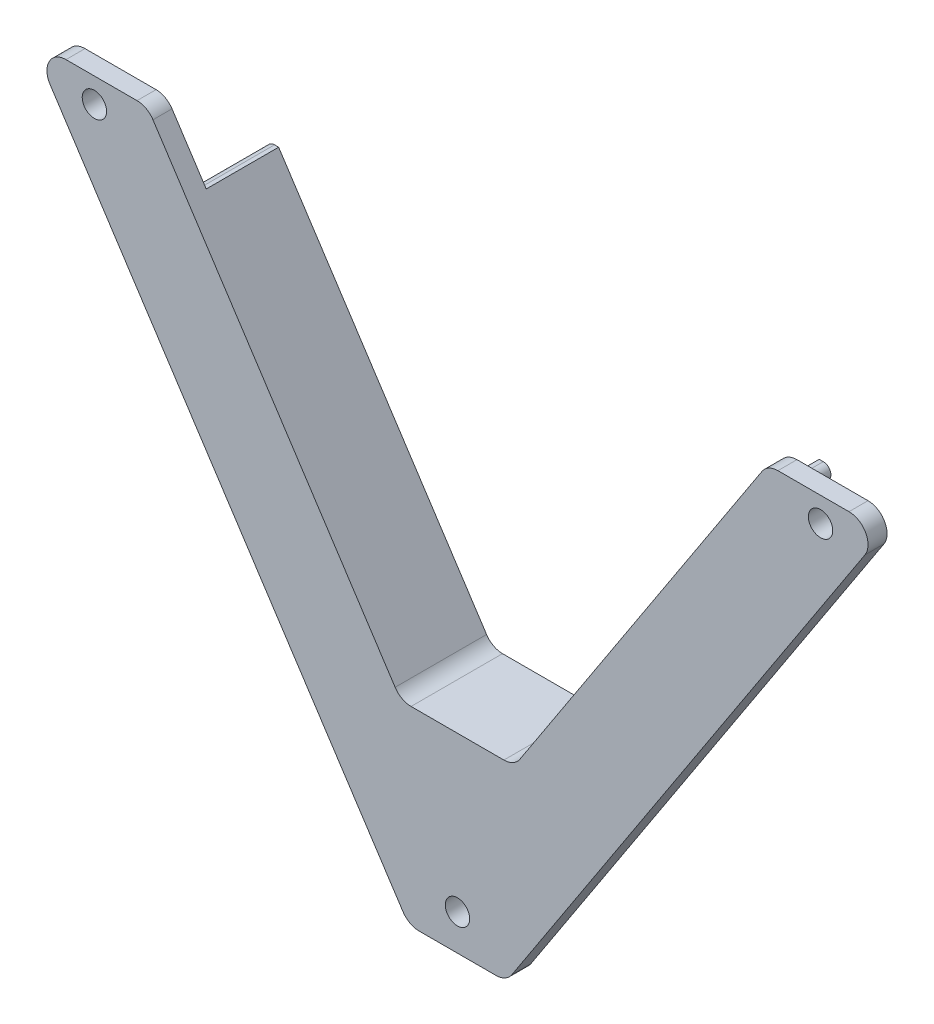
SolidWorks part; units mm, degrees
ref_plane "Plan de face" through (0, 0, 0) normal (0, 0, 1) x (1, 0, 0)
ref_plane "Plan de dessus" through (0, 0, 0) normal (0, 1, 0) x (1, 0, 0)
ref_plane "Plan de droite" through (0, 0, 0) normal (1, 0, 0) x (0, 0, -1)
sketch "Esquisse1" plane through (0, 0, 0) normal (0, 0, 1) x (1, 0, 0)
  line L0 (6.1176, 0) -> (6.4, 0)
  line L1 (6.4, 0) -> (-6.4, 0)
  line L2 (-56, 75.87) -> (56, 75.87) construction
  line L3 (-6.4, 0) -> (-56, 75.87)
  line L4 (0, 0) -> (0, 75.87) construction
  line L5 (6.4, 0) -> (56, 75.87)
  line L6 (-56, 75.87) -> (-40.7, 75.87)
  line L7 (-40.7, 75.87) -> (-7.4437, 25)
  line L8 (-7.4437, 25) -> (7.4437, 25)
  line L9 (7.4437, 25) -> (40.7, 75.87)
  line L10 (40.7, 75.87) -> (56, 75.87)
  point P8 (0, 0)
  dimension "D1" = 75.87
  dimension "D2" = 112
  dimension "D3" = 12.8
  dimension "D4" = 25
  dimension "D5" = 15.3
extrude "Boss.-Extru.1" add sketch "Esquisse1" along normal blind 2.5 contours L10 L9 L8 L7 L6 L3 L1 L0 L5
sketch "Esquisse2" plane through (0, 0, 2.5) normal (0, 0, 1) x (1, 0, 0)
  line L0 (0, 25) -> (0, 0) construction
  line L1 (-7.4437, 25) -> (7.4437, 25) construction
  line L2 (6.4, 0) -> (-6.4, 0) construction
  circle A0 centre (0, 4.7) radius 1.6
  dimension "D2" = 3.2
  dimension "D1" = 4.7
extrude "Enlèv. mat.-Extru.1" cut sketch "Esquisse2" against normal through all
sketch "Esquisse3" plane through (0, 0, 0) normal (0, 0, -1) x (-1, 0, 0)
  line L0 (-35.47, 67.87) -> (-7.4437, 25)
  line L1 (-7.4437, 25) -> (-40.7, 75.87) construction
  line L2 (-7.4437, 25) -> (7.4437, 25)
  line L3 (7.4437, 25) -> (35.47, 67.87)
  line L4 (40.7, 75.87) -> (7.4437, 25) construction
  line L5 (35.47, 67.87) -> (37.8595, 67.87)
  line L6 (37.8595, 67.87) -> (8.5257, 23)
  line L7 (8.5257, 23) -> (-8.5257, 23)
  line L8 (-8.5257, 23) -> (-37.8595, 67.87)
  line L9 (-37.8595, 67.87) -> (-35.47, 67.87)
  line L10 (0, 25) -> (0, 0) construction
  line L11 (-40.7, 75.87) -> (-56, 75.87) construction
  dimension "D1" = 8
  dimension "D2" = 2
  dimension "D3" = 2
extrude "Boss.-Extru.2" add sketch "Esquisse3" along normal blind 9.5
fillet "Congé2" radius 1 2 edges at (-37.8595, 67.87, -4.75) (37.8595, 67.87, -4.75)
fillet "Congé1" radius 2.5 8 edges at (40.7, 75.87, 1.25) (56, 75.87, 1.25) (-40.7, 75.87, 1.25) (-56, 75.87, 1.25) (6.4, 0, 1.25) (-6.4, 0, 1.25) (-7.4437, 25, -3.5) (7.4437, 25, -3.5)
sketch "Esquisse4" plane through (0, 0, 2.5) normal (0, 0, 1) x (1, 0, 0)
  line L0 (0, 25) -> (0, 0) construction
  line L1 (-6.0913, 25) -> (6.0913, 25) construction
  line L2 (5.0475, 0) -> (-5.0475, 0) construction
  line L3 (42.0525, 75.87) -> (51.3788, 75.87) construction
  line L4 (7.1401, 1.132) -> (53.4713, 72.002) construction
  circle A0 centre (47.6471, 72.6443) radius 1.6
  circle A1 centre (-47.6471, 72.6443) radius 1.6
  point P11 (0, 0)
  dimension "D1" = 3.2
  dimension "D2" = 3.2257
  dimension "D3" = 5.2264
extrude "Enlèv. mat.-Extru.2" cut sketch "Esquisse4" against normal through all
